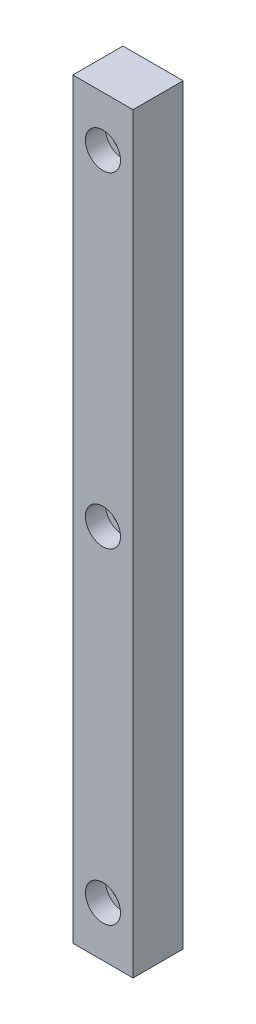
SolidWorks part; units mm, degrees
ref_plane "Alzado" through (0, 0, 0) normal (0, 0, 1) x (1, 0, 0)
ref_plane "Planta" through (0, 0, 0) normal (0, 1, 0) x (1, 0, 0)
ref_plane "Vista lateral" through (0, 0, 0) normal (1, 0, 0) x (0, 0, -1)
sketch "Croquis1" plane through (0, 0, 0) normal (0, 0, 1) x (1, 0, 0)
  line L1 (6, -75) -> (-6, -75)
  line L2 (6, -75) -> (6, 75)
  line L3 (6, 75) -> (-6, 75)
  line L4 (-6, -75) -> (-6, 75)
  line L5 (6, -75) -> (-6, 75) construction
  line L6 (6, 75) -> (-6, -75) construction
  circle A0 centre (0, 65) radius 2.25
  circle A1 centre (0, 0) radius 2.25
  circle A2 centre (0, -65) radius 2.25
  point P0 (0, 0)
  dimension "D3" = 4.5
  dimension "D1" = 12
  dimension "D2" = 150
  dimension "D4" = 10
  dimension "D5" = 10
extrude "Saliente-Extruir1" add sketch "Croquis1" along normal blind 10
sketch "Croquis2" plane through (0, 0, 10) normal (0, 0, 1) x (1, 0, 0)
  circle A0 centre (0, 65) radius 3.5
  circle A1 centre (0, 0) radius 3.5
  circle A2 centre (0, -65) radius 3.5
  dimension "D1" = 7
extrude "Cortar-Extruir1" cut sketch "Croquis2" against normal blind 4
